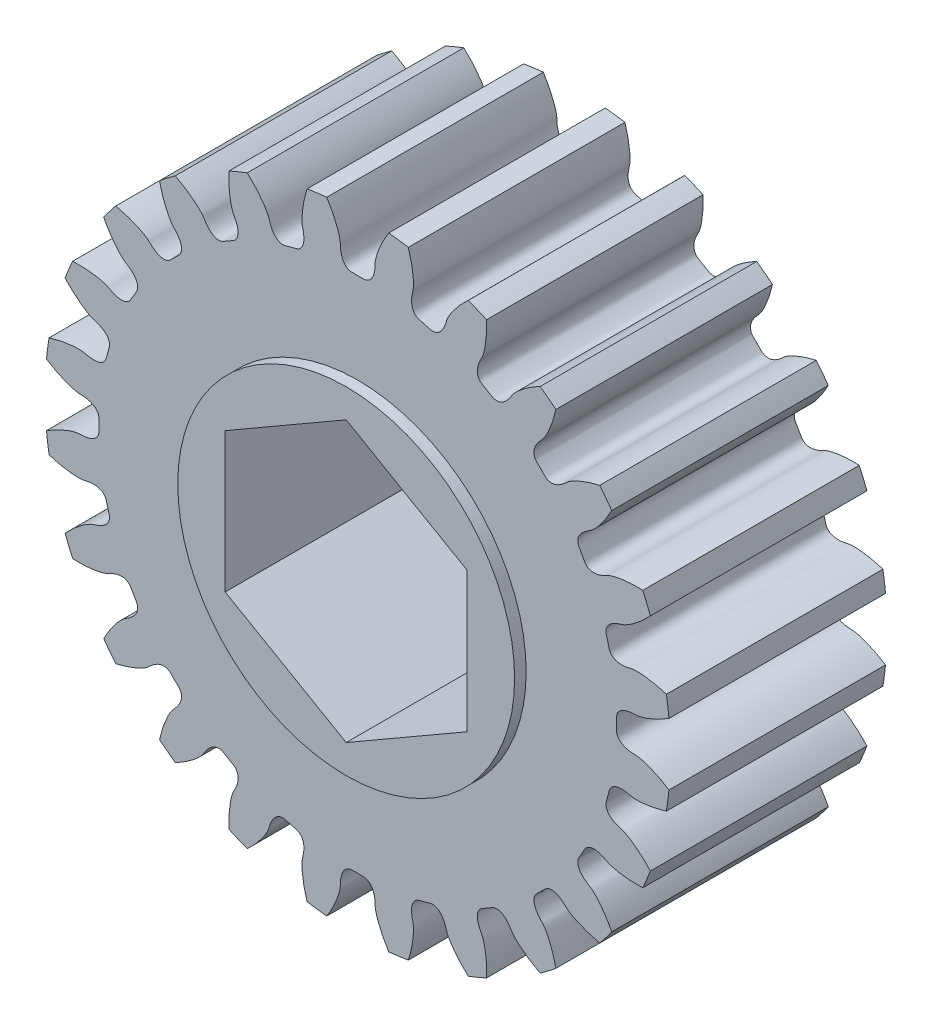
SolidWorks part; units mm, degrees
ref_plane "Front Plane" through (0, 0, 0) normal (0, 0, 1) x (1, 0, 0)
ref_plane "Top Plane" through (0, 0, 0) normal (0, 1, 0) x (1, 0, 0)
ref_plane "Right Plane" through (0, 0, 0) normal (1, 0, 0) x (0, 0, -1)
ref_plane "Plane1" through (0, 0, -5.715) normal (0, 0, -1) x (-1, 0, 0)
sketch "Sketch1" plane through (0, 0, -5.715) normal (0, 0, -1) x (-1, 0, 0)
  arc A0 (-12.7729, 10.461) -> (-13.4104, 9.6302) centre (0, 0) ccw
  arc A1 (-15.0452, 6.7987) -> (-15.446, 5.8312) centre (0, 0) ccw
  arc A2 (-16.2922, 2.673) -> (-16.4289, 1.6348) centre (0, 0) ccw
  arc A3 (-16.4289, -1.6348) -> (-16.2922, -2.673) centre (0, 0) ccw
  arc A4 (-15.446, -5.8312) -> (-15.0452, -6.7987) centre (0, 0) ccw
  arc A5 (-13.4104, -9.6302) -> (-12.7729, -10.461) centre (0, 0) ccw
  arc A6 (-10.461, -12.7729) -> (-9.6302, -13.4104) centre (0, 0) ccw
  arc A7 (-6.7987, -15.0452) -> (-5.8312, -15.446) centre (0, 0) ccw
  arc A8 (-2.673, -16.2922) -> (-1.6348, -16.4289) centre (0, 0) ccw
  arc A9 (1.6348, -16.4289) -> (2.673, -16.2922) centre (0, 0) ccw
  arc A10 (5.8312, -15.446) -> (6.7987, -15.0452) centre (0, 0) ccw
  arc A11 (9.6302, -13.4104) -> (10.461, -12.7729) centre (0, 0) ccw
  arc A12 (12.7729, -10.461) -> (13.4104, -9.6302) centre (0, 0) ccw
  arc A13 (15.0452, -6.7987) -> (15.446, -5.8312) centre (0, 0) ccw
  arc A14 (16.2922, -2.673) -> (16.4289, -1.6348) centre (0, 0) ccw
  arc A15 (16.4289, 1.6348) -> (16.2922, 2.673) centre (0, 0) ccw
  arc A16 (15.446, 5.8312) -> (15.0452, 6.7987) centre (0, 0) ccw
  arc A17 (13.4104, 9.6302) -> (12.7729, 10.461) centre (0, 0) ccw
  arc A18 (10.461, 12.7729) -> (9.6302, 13.4104) centre (0, 0) ccw
  arc A19 (6.7987, 15.0452) -> (5.8312, 15.446) centre (0, 0) ccw
  arc A20 (2.673, 16.2922) -> (1.6348, 16.4289) centre (0, 0) ccw
  arc A21 (-1.6348, 16.4289) -> (-2.673, 16.2922) centre (0, 0) ccw
  arc A22 (-5.8312, 15.446) -> (-6.7987, 15.0452) centre (0, 0) ccw
  arc A23 (-9.6302, 13.4104) -> (-10.461, 12.7729) centre (0, 0) ccw
  spline S0 degree 3 number of poles 101 (-15.0452, 6.7987) -> (-13.4104, 9.6302)
  spline S1 degree 3 number of poles 101 (-16.2922, 2.673) -> (-15.446, 5.8312)
  spline S2 degree 3 number of poles 101 (-16.4289, -1.6348) -> (-16.4289, 1.6348)
  spline S3 degree 3 number of poles 101 (-15.446, -5.8312) -> (-16.2922, -2.673)
  spline S4 degree 3 number of poles 101 (-13.4104, -9.6302) -> (-15.0452, -6.7987)
  spline S5 degree 3 number of poles 101 (-10.461, -12.7729) -> (-12.7729, -10.461)
  spline S6 degree 3 number of poles 101 (-6.7987, -15.0452) -> (-9.6302, -13.4104)
  spline S7 degree 3 number of poles 101 (-2.673, -16.2922) -> (-5.8312, -15.446)
  spline S8 degree 3 number of poles 101 (1.6348, -16.4289) -> (-1.6348, -16.4289)
  spline S9 degree 3 number of poles 101 (5.8312, -15.446) -> (2.673, -16.2922)
  spline S10 degree 3 number of poles 101 (9.6302, -13.4104) -> (6.7987, -15.0452)
  spline S11 degree 3 number of poles 101 (12.7729, -10.461) -> (10.461, -12.7729)
  spline S12 degree 3 number of poles 101 (15.0452, -6.7987) -> (13.4104, -9.6302)
  spline S13 degree 3 number of poles 101 (16.2922, -2.673) -> (15.446, -5.8312)
  spline S14 degree 3 number of poles 101 (16.4289, 1.6348) -> (16.4289, -1.6348)
  spline S15 degree 3 number of poles 101 (15.446, 5.8312) -> (16.2922, 2.673)
  spline S16 degree 3 number of poles 101 (13.4104, 9.6302) -> (15.0452, 6.7987)
  spline S17 degree 3 number of poles 101 (10.461, 12.7729) -> (12.7729, 10.461)
  spline S18 degree 3 number of poles 101 (6.7987, 15.0452) -> (9.6302, 13.4104)
  spline S19 degree 3 number of poles 101 (2.673, 16.2922) -> (5.8312, 15.446)
  spline S20 degree 3 number of poles 101 (-1.6348, 16.4289) -> (1.6348, 16.4289)
  spline S21 degree 3 number of poles 101 (-5.8312, 15.446) -> (-2.673, 16.2922)
  spline S22 degree 3 number of poles 101 (-9.6302, 13.4104) -> (-6.7987, 15.0452)
  spline S23 degree 3 number of poles 101 (-12.7729, 10.461) -> (-10.461, 12.7729)
extrude "Boss-Extrude1" add sketch "Sketch1" against normal blind 11.43
sketch "Sketch2" plane through (0, 0, -5.715) normal (0, 0, -1) x (-1, 0, 0)
  circle A0 centre (0, 0) radius 8.89
extrude "Boss-Extrude2" add sketch "Sketch2" along normal blind 0.6096
sketch "Sketch3" plane through (0, 0, 5.715) normal (0, 0, 1) x (1, 0, 0)
  circle A0 centre (0, 0) radius 8.89
extrude "Boss-Extrude3" add sketch "Sketch3" along normal blind 0.6096
sketch "Sketch4" plane through (0, 0, 6.3246) normal (0, 0, 1) x (1, 0, 0)
  line L0 (6.3881, -3.6882) -> (6.3881, 3.6882)
  line L1 (6.3881, 3.6882) -> (0, 7.3763)
  line L2 (0, 7.3763) -> (-6.3881, 3.6882)
  line L3 (-6.3881, 3.6882) -> (-6.3881, -3.6882)
  line L4 (-6.3881, -3.6882) -> (0, -7.3763)
  line L5 (0, -7.3763) -> (6.3881, -3.6882)
extrude "Cut-Extrude1" cut sketch "Sketch4" against normal through all
